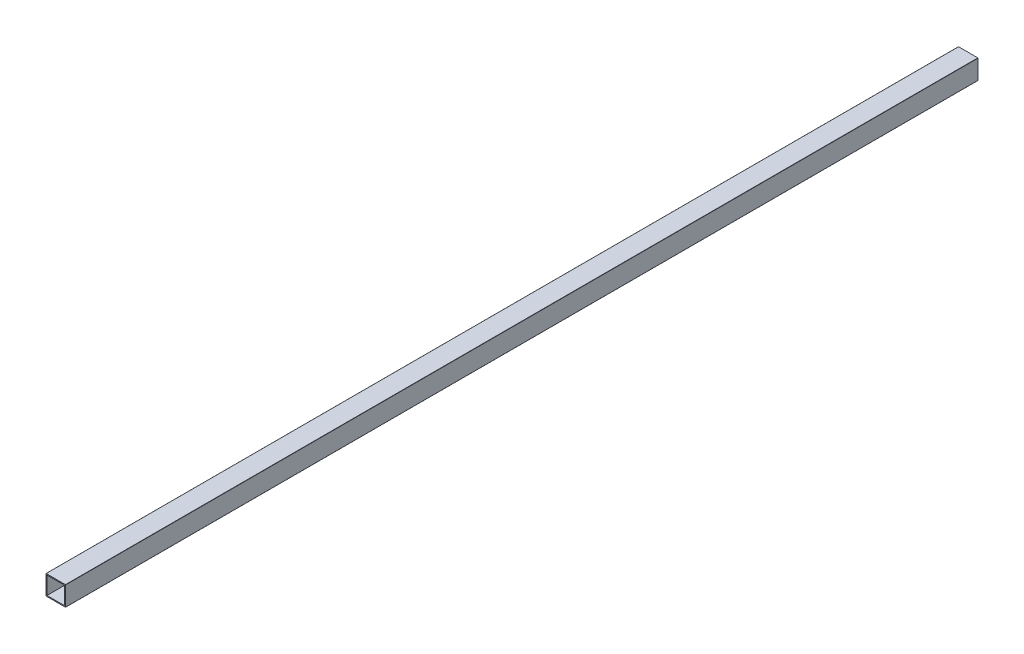
SolidWorks part; units mm, degrees
ref_plane "Front Plane" through (0, 0, 0) normal (0, 0, 1) x (1, 0, 0)
ref_plane "Top Plane" through (0, 0, 0) normal (0, 1, 0) x (1, 0, 0)
ref_plane "Right Plane" through (0, 0, 0) normal (1, 0, 0) x (0, 0, -1)
sketch "Sketch1" plane through (0, 0, 0) normal (0, 0, 1) x (1, 0, 0)
  line L0 (1, 1) -> (19, 1)
  line L1 (0.2, 0) -> (19.8, 0)
  line L2 (0, 0.2) -> (0, 19.8)
  line L3 (0.2, 20) -> (19.8, 20)
  line L4 (20, 0.2) -> (20, 19.8)
  line L5 (19, 1) -> (19, 19)
  line L6 (1, 19) -> (19, 19)
  line L7 (1, 1) -> (1, 19)
  arc A0 (0.2, 0) -> (0, 0.2) centre (0.2, 0.2) cw
  arc A1 (19.8, 0) -> (20, 0.2) centre (19.8, 0.2) ccw
  arc A2 (19.8, 20) -> (20, 19.8) centre (19.8, 19.8) cw
  arc A3 (0, 19.8) -> (0.2, 20) centre (0.2, 19.8) cw
  arc A4 (19, 1) -> (19, 1) centre (19, 1) ccw
  arc A5 (19, 19) -> (19, 19) centre (19, 19) cw
  arc A6 (1, 19) -> (1, 19) centre (1, 19) cw
  arc A7 (1, 1) -> (1, 1) centre (1, 1) cw
  point P7 (0, 0)
  point P10 (20, 0)
  point P13 (20, 20)
  point P16 (0, 20)
  dimension "fillet" = 0.2
  dimension "width" = 20
  dimension "height" = 20
  dimension "thickness" = 1
extrude "Boss-Extrude1" add sketch "Sketch1" along normal blind 930
sketch "Sketch2" plane through (0, 0, 0) normal (-1, 0, 0) x (0, 0, 1)
  line L0 (0, 20) -> (19.7136, 20)
  line L1 (930, 20) -> (0, 20) construction
  line L2 (19.7136, 20) -> (0, 0)
  line L3 (0, 0) -> (0, 20)
  line L18 (930, 0) -> (909.7094, 20)
  line L19 (909.7094, 20) -> (930, 20)
  line L20 (930, 20) -> (930, 0)
  dimension "Skew2" = 90
  dimension "Skew1" = 45.413
extrude "Skew Cut" [suppressed] cut sketch "Sketch2" against normal through all
sketch "Sketch3" plane through (0, 0, 0) normal (-1, 0, 0) x (0, 0, 1)
  line L0 (11.547, 20) -> (0, 0)
  line L2 (930, 20) -> (0, 20) construction
  line L3 (0, 0) -> (0, 20)
  line L4 (0, 20) -> (11.547, 20)
  dimension "Skew3" = 30
extrude "Cut-Extrude2" [suppressed] cut sketch "Sketch3" against normal through all
sketch "Sketch4" plane through (0, 0, 0) normal (-1, 0, 0) x (0, 0, 1)
  line L0 (779.441, 10.2) -> (680.25, 10.2) construction
  line L1 (779.441, 3.45) -> (680.25, 3.45)
  line L2 (779.441, 16.95) -> (680.25, 16.95)
  line L3 (0, 19.8) -> (0, 0.2) construction
  line L4 (930, 0) -> (0, 0) construction
  line L6 (299.441, 10.2) -> (200.25, 10.2) construction
  line L8 (299.441, 3.45) -> (200.25, 3.45)
  line L11 (299.441, 16.95) -> (200.25, 16.95)
  arc A0 (779.441, 3.45) -> (779.441, 16.95) centre (779.441, 10.2) ccw
  arc A1 (680.25, 16.95) -> (680.25, 3.45) centre (680.25, 10.2) ccw
  arc A4 (299.441, 3.45) -> (299.441, 16.95) centre (299.441, 10.2) ccw
  arc A5 (200.25, 16.95) -> (200.25, 3.45) centre (200.25, 10.2) ccw
  point P2 (729.8455, 10.2)
  point P9 (0, 0)
  point P14 (249.8455, 10.2)
  dimension "D3" = 6.75
  dimension "D4" = 200.25
  dimension "D1" = 10.2
  dimension "D2" = 99.191
  dimension "D5" = 2
extrude "Cut-Extrude3" [suppressed] cut sketch "Sketch4" against normal blind 10
sketch "Sketch5" plane through (0, 20, 0) normal (0, 1, 0) x (1, 0, 0)
  line L0 (0, -930) -> (0, 0) construction
  line L1 (5.4496, -270.25) -> (15.4496, -270.25)
  line L2 (5.4496, -270.25) -> (5.4496, -331.75)
  line L3 (5.4496, -331.75) -> (15.4496, -331.75)
  line L4 (15.4496, -270.25) -> (15.4496, -331.75)
  line L5 (5.4496, -750.25) -> (15.4496, -750.25)
  line L10 (5.4496, -750.25) -> (5.4496, -811.75)
  line L11 (5.4496, -811.75) -> (15.4496, -811.75)
  line L12 (15.4496, -750.25) -> (15.4496, -811.75)
  point P6 (0, 0)
  point P12 (0, -480)
  dimension "D1" = 5.4496
  dimension "D2" = 10
  dimension "D3" = 61.5
  dimension "D4" = 270.25
  dimension "D5" = 2
extrude "Cut-Extrude4" [suppressed] cut sketch "Sketch5" against normal blind 10
sketch "Sketch6" [suppressed] plane through (20, 0, 0) normal (1, 0, 0) x (0, 0, -1)
  line L0 (-35, 0.2) -> (-35, 19.8) construction
  circle A0 centre (105, 10) radius 2.5
  circle A1 centre (-15, 10) radius 2.5
  dimension "D2" = 160
  dimension "D3" = 5
  dimension "D1" = 20
extrude "Cut-Extrude5" [suppressed] cut sketch "Sketch6" against normal through all
sketch "Sketch7" [suppressed] plane through (0, 10, 0) normal (0, 1, 0) x (1, 0, 0)
  line L0 (0.2, -110) -> (9.8, -110) construction
  line L1 (0.2, -220) -> (0.2, 0) construction
  line L2 (9.8, -220) -> (9.8, 0) construction
  line L3 (9.8, 0) -> (0.2, 0) construction
  circle A0 centre (5, -50) radius 2.15
  circle A1 centre (5, -170) radius 2.15
  point P9 (5, -110)
  point P14 (5, 0)
  dimension "D1" = 4.3
  dimension "D2" = 60
extrude "Cut-Extrude6" [suppressed] cut sketch "Sketch7" against normal through all
sketch "Sketch8" [suppressed] plane through (0, 0, 0) normal (0, -1, 0) x (1, 0, 0)
  line L0 (0.2, 210) -> (9.8, 210) construction
  circle A0 centre (5, 170) radius 2.15
  circle A1 centre (5, 45) radius 2.15
  point P6 (5, 210)
  dimension "D1" = 4.3
  dimension "D2" = 40
  dimension "D3" = 125
extrude "Cut-Extrude7" [suppressed] cut sketch "Sketch8" against normal through all
